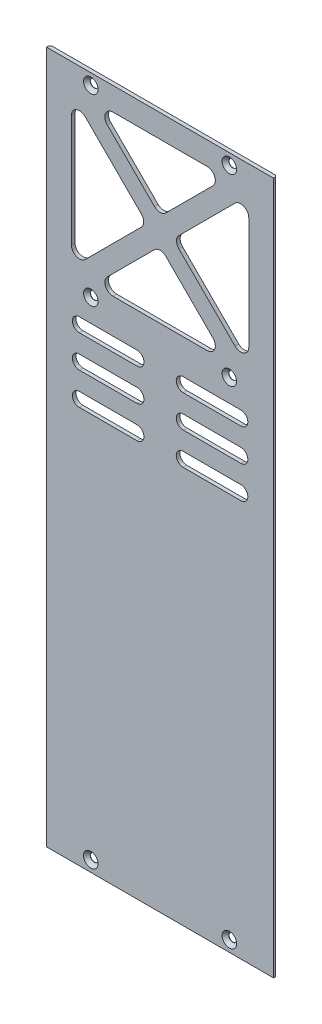
SolidWorks part; units mm, degrees
material "6061-T6 (SS)"
ref_plane "Front Plane" through (0, 0, 0) normal (0, 0, 1) x (1, 0, 0)
ref_plane "Top Plane" through (0, 0, 0) normal (0, 1, 0) x (1, 0, 0)
ref_plane "Right Plane" through (0, 0, 0) normal (1, 0, 0) x (0, 0, -1)
sketch "Sketch1" plane through (0, 0, 0) normal (0, 0, 1) x (1, 0, 0)
  line L1 (49.2063, -150) -> (-49.2062, -150)
  line L2 (49.2063, -150) -> (49.2063, 150)
  line L3 (49.2063, 150) -> (-49.2062, 150)
  line L4 (-49.2062, -150) -> (-49.2062, 150)
  line L5 (49.2063, -150) -> (-49.2062, 150) construction
  line L6 (49.2063, 150) -> (-49.2062, -150) construction
  point P0 (0, 0)
  dimension "D1" = 300
  dimension "D2" = 98.4125
extrude "Boss-Extrude1" add sketch "Sketch1" along normal mid plane 1.5875
chamfer "Chamfer1" distance 0.7937 angle 45 4 edges at (0, -150, -0.7937) (-49.2062, 0, -0.7937) (0, 150, -0.7937) (49.2063, 0, -0.7937)
sketch "Sketch2" plane through (0, 0, -0.7937) normal (0, 0, -1) x (-1, 0, 0)
  line L1 (0, 111.1319) -> (28.8681, 140)
  line L2 (28.8681, 140) -> (-28.8681, 140)
  line L4 (-38.4125, 138.2306) -> (-5.6569, 105.475)
  line L5 (-5.6569, 105.475) -> (-38.4125, 72.7194)
  line L6 (-38.4125, 72.7194) -> (-38.4125, 138.2306)
  line L7 (-28.8681, 70.95) -> (28.8681, 70.95)
  line L8 (28.8681, 70.95) -> (0, 99.8181)
  line L9 (0, 99.8181) -> (-28.8681, 70.95)
  line L10 (38.4125, 72.7194) -> (5.6569, 105.475)
  line L11 (5.6569, 105.475) -> (38.4125, 138.2306)
  line L12 (38.4125, 138.2306) -> (38.4125, 72.7194)
  line L13 (-48.4125, 150) -> (48.4125, 150) construction
  line L14 (-48.4125, 150) -> (-48.4125, -150) construction
  line L15 (48.4125, -150) -> (48.4125, 150) construction
  line L16 (-28.8681, 140) -> (0, 111.1319)
  line L17 (0, 99.8181) -> (0, 111.1319)
  line L18 (-5.6569, 105.475) -> (5.6569, 105.475)
  line L19 (-35, 52.95) -> (-10, 52.95) construction
  line L20 (-35, 55.95) -> (-10, 55.95)
  line L21 (-35, 49.95) -> (-10, 49.95)
  line L22 (-35, 38.95) -> (-10, 38.95) construction
  line L23 (-35, 41.95) -> (-10, 41.95)
  line L24 (-35, 35.95) -> (-10, 35.95)
  line L25 (-35, 24.95) -> (-10, 24.95) construction
  line L26 (-35, 27.95) -> (-10, 27.95)
  line L27 (-35, 21.95) -> (-10, 21.95)
  line L28 (10, 52.95) -> (35, 52.95) construction
  line L29 (10, 55.95) -> (35, 55.95)
  line L30 (10, 49.95) -> (35, 49.95)
  line L31 (10, 38.95) -> (35, 38.95) construction
  line L32 (10, 41.95) -> (35, 41.95)
  line L33 (10, 35.95) -> (35, 35.95)
  line L34 (10, 24.95) -> (35, 24.95) construction
  line L35 (10, 27.95) -> (35, 27.95)
  line L36 (10, 21.95) -> (35, 21.95)
  arc A0 (-35, 55.95) -> (-35, 49.95) centre (-35, 52.95) ccw
  arc A1 (-10, 49.95) -> (-10, 55.95) centre (-10, 52.95) ccw
  arc A2 (-35, 41.95) -> (-35, 35.95) centre (-35, 38.95) ccw
  arc A3 (-10, 35.95) -> (-10, 41.95) centre (-10, 38.95) ccw
  arc A4 (-35, 27.95) -> (-35, 21.95) centre (-35, 24.95) ccw
  arc A5 (-10, 21.95) -> (-10, 27.95) centre (-10, 24.95) ccw
  arc A6 (10, 55.95) -> (10, 49.95) centre (10, 52.95) ccw
  arc A7 (35, 49.95) -> (35, 55.95) centre (35, 52.95) ccw
  arc A8 (10, 41.95) -> (10, 35.95) centre (10, 38.95) ccw
  arc A9 (35, 35.95) -> (35, 41.95) centre (35, 38.95) ccw
  arc A10 (10, 27.95) -> (10, 21.95) centre (10, 24.95) ccw
  arc A11 (35, 21.95) -> (35, 27.95) centre (35, 24.95) ccw
  point P12 (-22.5, 52.95)
  point P25 (-22.5, 38.95)
  point P32 (-22.5, 24.95)
  point P39 (22.5, 52.95)
  point P46 (22.5, 38.95)
  point P53 (22.5, 24.95)
  dimension "D9" = 3
  dimension "D1" = 10
  dimension "D2" = 10
  dimension "D3" = 10
  dimension "D4" = 79.05
  dimension "D5" = 8
  dimension "D6" = 8
  dimension "D7" = 8
  dimension "D8" = 25
  dimension "D10" = 20
  dimension "D11" = 10
  dimension "D12" = 8
  dimension "D13" = 8
  dimension "D14" = 15
extrude "Cut-Extrude1" cut sketch "Sketch2" against normal through all contours L8 L9 L7 | L6 L5 L4 | L2 L16 L1 | L12 L11 L10 | L30 A7 L29 A6 | L27 A5 L26 A4 | L20 A1 L21 A0 | L23 A3 L24 A2 | L32 A9 L33 A8 | L35 A11 L36 A10
fillet "Fillet1" radius 3.5 12 edges at (-5.6569, 105.475, 0) (-38.4125, 138.2306, 0) (-28.8681, 140, 0) (0, 111.1319, 0) (28.8681, 140, 0) (38.4125, 138.2306, 0) (5.6569, 105.475, 0) (-28.8681, 70.95, 0) (0, 99.8181, 0) (-38.4125, 72.7194, 0) (28.8681, 70.95, 0) (38.4125, 72.7194, 0)
hole_wizard "CSK for M3 Flat Head Machine Screw1" positions "Sketch5" profile "Sketch4" countersink size "M3" standard "ANSI Metric"
sketch "Sketch5" plane through (0, 0, 0.7937) normal (0, 0, 1) x (1, 0, 0)
  line L0 (-49.2062, -150) -> (49.2063, -150) construction
  line L1 (49.2063, 150) -> (-49.2062, 150) construction
  point P0 (-30, -145.225)
  point P2 (30, -145.225)
  point P4 (-30, 65.7)
  point P6 (30, 65.7)
  point P8 (30, 145.225)
  point P10 (-30, 145.225)
  dimension "D1" = 30
  dimension "D2" = 30
  dimension "D3" = 4.775
  dimension "D4" = 4.775
  dimension "D5" = 79.525
sketch "Sketch4" plane through (-30, -145.225, 0.7937) normal (1, 0, 0) x (0, -1, 0)
  line L0 (0, 0) -> (0, 8.6175)
  line L1 (0, 8.6175) -> (1.7, 7.596)
  line L2 (1.7, 7.596) -> (1.7, 1.45)
  line L3 (1.7, 1.45) -> (3.15, 0)
  line L5 (3.15, 0) -> (0, 0)
  line L6 (-1.7, 1.45) -> (-3.15, 0) construction
  line L10 (0, 8.6175) -> (-1.7, 7.596) construction
  line L11 (0, -6.35) -> (0, 107.95) construction
  dimension "Hole Dia." = 3.4
  dimension "Hole Depth" = 7.596
  dimension "Near C'Sink Dia." = 6.3
  dimension "Near C'Sink Angle" = 90
  dimension "Drill Angle" = 118
